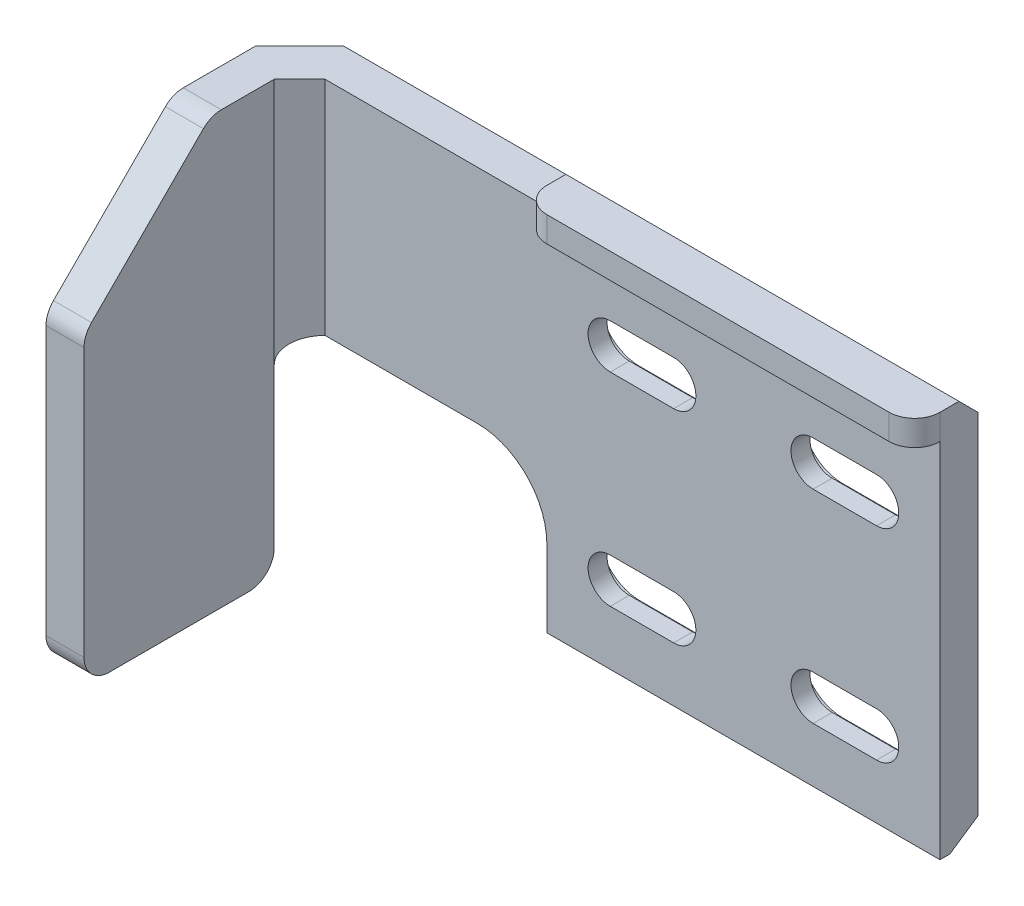
SolidWorks part; units mm, degrees
ref_plane "Front Plane" through (0, 0, 0) normal (0, 0, 1) x (1, 0, 0)
ref_plane "Top Plane" through (0, 0, 0) normal (0, 1, 0) x (1, 0, 0)
ref_plane "Right Plane" through (0, 0, 0) normal (1, 0, 0) x (0, 0, -1)
sketch "Sketch1" plane through (0, 0, 0) normal (0, 0, 1) x (1, 0, 0)
  line L0 (0, 15.9158) -> (0, -13.0842) construction
  line L5 (-25, 15.9158) -> (25, 15.9158) construction
  line L7 (-8, 31.9158) -> (8, 31.9158) construction
  line L8 (-8, 31.9158) -> (-8, 15.9158) construction
  line L9 (-8, 15.9158) -> (8, 15.9158) construction
  line L10 (8, 31.9158) -> (8, 15.9158) construction
  line L11 (-8, 31.9158) -> (8, 15.9158) construction
  line L12 (-8, 15.9158) -> (8, 31.9158) construction
  line L13 (-8, -13.0842) -> (8, -13.0842) construction
  line L14 (-8, -13.0842) -> (-8, -29.0842) construction
  line L15 (-8, -29.0842) -> (8, -29.0842) construction
  line L16 (8, -13.0842) -> (8, -29.0842) construction
  line L17 (-8, -13.0842) -> (8, -29.0842) construction
  line L18 (-8, -29.0842) -> (8, -13.0842) construction
  line L19 (0, -13.0842) -> (0, -16.0842) construction
  line L20 (-16.5, -16.0842) -> (16.5, -16.0842) construction
  line L21 (-25, 15.9158) -> (-25, -16.0842) construction
  line L22 (-25, -16.0842) -> (-16.5, -16.0842) construction
  line L23 (-8, 31.9158) -> (-38, 31.9158) construction
  line L24 (38, 38.9158) -> (-38, 38.9158)
  line L25 (38, 38.9158) -> (38, -36.0842) construction
  line L26 (38, -36.0842) -> (-38, -36.0842) construction
  line L27 (-38, 38.9158) -> (-38, -36.0842) construction
  line L28 (8, 31.9158) -> (38, 31.9158) construction
  line L29 (8, 31.9158) -> (8, 38.9158) construction
  line L30 (8, -29.0842) -> (8, -36.0842) construction
  line L31 (-10.5, 31.9158) -> (-5.5, 31.9158) construction
  line L34 (-10.5, 33.6658) -> (-5.5, 33.6658)
  line L37 (-10.5, 30.1658) -> (-5.5, 30.1658)
  line L38 (5.5, 31.9158) -> (10.5, 31.9158) construction
  line L39 (5.5, 33.6658) -> (10.5, 33.6658)
  line L40 (5.5, 30.1658) -> (10.5, 30.1658)
  line L41 (5.5, 15.9158) -> (10.5, 15.9158) construction
  line L42 (5.5, 17.6658) -> (10.5, 17.6658)
  line L43 (5.5, 14.1658) -> (10.5, 14.1658)
  line L44 (-10.5, 15.9158) -> (-5.5, 15.9158) construction
  line L45 (-10.5, 17.6658) -> (-5.5, 17.6658)
  line L46 (-10.5, 14.1658) -> (-5.5, 14.1658)
  line L47 (-38, 38.9158) -> (-38, 9.8549)
  line L48 (-38, 9.8549) -> (38, 9.8549) construction
  line L49 (38, 9.8549) -> (38, 38.9158)
  line L50 (-36.8222, 31.9158) -> (-36.8222, 9.9158) construction
  line L51 (-29, 15.9158) -> (-21, 15.9158) construction
  line L54 (-29, 21.4158) -> (-21, 21.4158) construction
  line L57 (-29, 10.4158) -> (-21, 10.4158) construction
  line L58 (21, 15.9158) -> (29, 15.9158) construction
  line L59 (21, 21.4158) -> (29, 21.4158) construction
  line L60 (21, 10.4158) -> (29, 10.4158) construction
  line L61 (-29, 21.4158) -> (-21, 21.4158)
  line L62 (-34.5, 15.9158) -> (-34.5, 9.8549)
  line L63 (-34.5, 9.8549) -> (-38, 9.8549)
  line L64 (-15.5, 15.9158) -> (-15.5, 9.8549)
  line L65 (15.5, 15.9158) -> (15.5, 9.8549)
  line L66 (15.5, 9.8549) -> (-15.5, 9.8549)
  line L67 (34.5, 15.9158) -> (34.5, 9.8549)
  line L68 (34.5, 9.8549) -> (38, 9.8549)
  line L69 (21, 21.4158) -> (29, 21.4158)
  line L70 (-29, 21.4158) -> (-34.5, 21.4158)
  line L71 (-34.5, 21.4158) -> (-34.5, 15.9158)
  line L72 (29, 21.4158) -> (34.5, 21.4158) construction
  line L73 (34.5, 21.4158) -> (34.5, 15.9158) construction
  circle A0 centre (-8, 31.9158) radius 1.75 construction
  circle A1 centre (8, 31.9158) radius 1.75 construction
  circle A2 centre (8, 15.9158) radius 1.75 construction
  circle A3 centre (-8, 15.9158) radius 1.75 construction
  circle A4 centre (-8, -13.0842) radius 1.75 construction
  circle A5 centre (8, -13.0842) radius 1.75 construction
  circle A6 centre (8, -29.0842) radius 1.75 construction
  circle A7 centre (-8, -29.0842) radius 1.75 construction
  circle A8 centre (-25, 15.9158) radius 5.5 construction
  circle A9 centre (25, 15.9158) radius 5.5 construction
  circle A10 centre (-16.5, -16.0842) radius 5.5 construction
  circle A11 centre (16.5, -16.0842) radius 5.5 construction
  arc A16 (-10.5, 33.6658) -> (-10.5, 30.1658) centre (-10.5, 31.9158) ccw
  arc A17 (-5.5, 30.1658) -> (-5.5, 33.6658) centre (-5.5, 31.9158) ccw
  arc A18 (5.5, 33.6658) -> (5.5, 30.1658) centre (5.5, 31.9158) ccw
  arc A19 (10.5, 30.1658) -> (10.5, 33.6658) centre (10.5, 31.9158) ccw
  arc A20 (5.5, 17.6658) -> (5.5, 14.1658) centre (5.5, 15.9158) ccw
  arc A21 (10.5, 14.1658) -> (10.5, 17.6658) centre (10.5, 15.9158) ccw
  arc A22 (-10.5, 17.6658) -> (-10.5, 14.1658) centre (-10.5, 15.9158) ccw
  arc A23 (-5.5, 14.1658) -> (-5.5, 17.6658) centre (-5.5, 15.9158) ccw
  arc A28 (-29, 21.4158) -> (-29, 10.4158) centre (-29, 15.9158) ccw construction
  arc A29 (-21, 10.4158) -> (-21, 21.4158) centre (-21, 15.9158) ccw construction
  arc A30 (21, 21.4158) -> (21, 10.4158) centre (21, 15.9158) ccw construction
  arc A31 (29, 10.4158) -> (29, 21.4158) centre (29, 15.9158) ccw construction
  arc A32 (21, 21.4158) -> (15.5, 15.9158) centre (21, 15.9158) ccw
  arc A34 (-21, 21.4158) -> (-15.5, 15.9158) centre (-21, 15.9158) cw
  arc A37 (29, 21.4158) -> (34.5, 15.9158) centre (29, 15.9158) cw
  point P5 (0, 15.9158)
  point P8 (0, 23.9158)
  point P13 (0, -21.0842)
  point P31 (0, -16.0842)
  point P42 (-8, 31.9158)
  point P49 (8, 31.9158)
  point P56 (8, 15.9158)
  point P63 (-8, 15.9158)
  point P75 (-25, 15.9158)
  point P81 (25, 15.9158)
  dimension "D2" = 3.5
  dimension "D5" = 11
  dimension "D11" = 76
  dimension "D12" = 22
  dimension "D1" = 16
  dimension "D3" = 29
  dimension "D4" = 32
  dimension "D6" = 30
  dimension "D7" = 75
  dimension "D8" = 7
  dimension "D9" = 33
  dimension "D10" = 50
extrude "Boss-Extrude1" add sketch "Sketch1" along normal blind 3
sketch "Sketch2" plane through (0, 0, 3) normal (0, 0, 1) x (1, 0, 0)
  line L0 (38, 38.9158) -> (-38, 38.9158) construction
  line L1 (-38, 38.9158) -> (-35, 38.9158)
  line L2 (-38, 38.9158) -> (-38, 4.9158)
  line L3 (-38, 4.9158) -> (-35, 4.9158)
  line L4 (-35, 38.9158) -> (-35, 4.9158)
  dimension "D1" = 34
  dimension "D2" = 3
extrude "Boss-Extrude2" add sketch "Sketch2" along normal blind 17 and the other way up to vertex (3 mm away) other way up to point (-38, 9.8549, 0)
sketch "Sketch3" plane through (0, 0, 3) normal (0, 0, 1) x (1, 0, 0)
  line L1 (38, 38.9158) -> (15.5, 38.9158)
  line L2 (38, 38.9158) -> (38, 9.8549)
  line L3 (38, 9.8549) -> (15.5, 9.8549)
  line L4 (15.5, 38.9158) -> (15.5, 9.8549)
extrude "Cut-Extrude1" cut sketch "Sketch3" against normal blind 18
sketch "Sketch4" plane through (0, 0, 0) normal (0, 0, -1) x (-1, 0, 0)
  line L0 (4.8, 31.9158) -> (11.2, 31.9158) construction
  line L1 (4.8, 35.1158) -> (11.2, 35.1158)
  line L2 (4.8, 28.7158) -> (11.2, 28.7158)
  line L3 (-8, 33.6658) -> (-8, 30.1658) construction
  line L4 (-10.5, 33.6658) -> (-5.5, 33.6658) construction
  line L5 (-5.5, 30.1658) -> (-10.5, 30.1658) construction
  line L6 (-8, 17.6658) -> (-8, 14.1658) construction
  line L7 (-10.5, 17.6658) -> (-5.5, 17.6658) construction
  line L8 (-5.5, 14.1658) -> (-10.5, 14.1658) construction
  line L9 (8, 33.6658) -> (8, 30.1658) construction
  line L10 (5.5, 33.6658) -> (10.5, 33.6658) construction
  line L11 (10.5, 30.1658) -> (5.5, 30.1658) construction
  line L12 (8, 17.6658) -> (8, 14.1658) construction
  line L13 (5.5, 17.6658) -> (10.5, 17.6658) construction
  line L14 (10.5, 14.1658) -> (5.5, 14.1658) construction
  line L15 (-11.2, 31.9158) -> (-4.8, 31.9158) construction
  line L16 (-11.2, 35.1158) -> (-4.8, 35.1158)
  line L17 (-11.2, 28.7158) -> (-4.8, 28.7158)
  line L18 (4.8, 15.9158) -> (11.2, 15.9158) construction
  line L19 (4.8, 19.1158) -> (11.2, 19.1158)
  line L20 (4.8, 12.7158) -> (11.2, 12.7158)
  line L21 (-11.2, 15.9158) -> (-4.8, 15.9158) construction
  line L22 (-11.2, 19.1158) -> (-4.8, 19.1158)
  line L23 (-11.2, 12.7158) -> (-4.8, 12.7158)
  arc A0 (4.8, 35.1158) -> (4.8, 28.7158) centre (4.8, 31.9158) ccw
  arc A1 (11.2, 28.7158) -> (11.2, 35.1158) centre (11.2, 31.9158) ccw
  arc A2 (-11.2, 35.1158) -> (-11.2, 28.7158) centre (-11.2, 31.9158) ccw
  arc A3 (-4.8, 28.7158) -> (-4.8, 35.1158) centre (-4.8, 31.9158) ccw
  arc A4 (4.8, 19.1158) -> (4.8, 12.7158) centre (4.8, 15.9158) ccw
  arc A5 (11.2, 12.7158) -> (11.2, 19.1158) centre (11.2, 15.9158) ccw
  arc A6 (-11.2, 19.1158) -> (-11.2, 12.7158) centre (-11.2, 15.9158) ccw
  arc A7 (-4.8, 12.7158) -> (-4.8, 19.1158) centre (-4.8, 15.9158) ccw
  point P2 (8, 31.9158)
  point P34 (-8, 31.9158)
  point P40 (8, 15.9158)
  point P47 (-8, 15.9158)
  dimension "D1" = 3.2
  dimension "D2" = 6.4
extrude "Cut-Extrude2" cut sketch "Sketch4" against normal blind 1.5
chamfer "Chamfer1" distance 10 angle 45 1 edges at (-36.5, 38.9158, 20)
chamfer "Chamfer2" distance 1.5 angle 56 1 edges at (0, 9.8549, 0)
sketch "Sketch7" plane through (0, 0, 3) normal (0, 0, 1) x (1, 0, 0)
  line L0 (-15.5, 9.8549) -> (-15.5, 38.4158) construction
  line L1 (15.5, 38.9158) -> (-15.5, 38.9158) construction
  line L2 (15.5, 38.9158) -> (15.5, 38.4158) construction
  line L3 (15.5, 38.4158) -> (-15.5, 38.4158) construction
  line L4 (-15.5, 38.9158) -> (-15.5, 38.4158) construction
  line L5 (-15.5, 38.4158) -> (15.5, 38.4158)
  line L6 (-15.5, 38.4158) -> (-15.5, 40.4158)
  line L7 (-15.5, 40.4158) -> (15.5, 40.4158)
  line L8 (15.5, 38.4158) -> (15.5, 40.4158)
  dimension "D1" = 0.5
  dimension "D2" = 2
  dimension "D3" = 31
extrude "Boss-Extrude3" add sketch "Sketch7" along normal blind 2 and the other way up to vertex (3 mm away)
sketch "Sketch9" plane through (0, 0, 0) normal (0, 0, -1) x (-1, 0, 0)
  line L1 (35, 9.8549) -> (34.5, 9.8549)
  line L2 (35, 9.8549) -> (35, 21.4158)
  line L3 (35, 21.4158) -> (34.5, 21.4158)
  line L4 (34.5, 9.8549) -> (34.5, 21.4158)
extrude "Cut-Extrude4" cut sketch "Sketch9" against normal blind 10
chamfer "Chamfer3" distance 1.5 angle 45 1 edges at (0, 40.4158, 0)
sketch "Sketch11" plane through (0, 4.9158, 0) normal (0, -1, 0) x (-1, 0, 0)
  line L0 (35, 0) -> (35, -20) construction
  line L1 (38, 0) -> (35, 0)
  line L2 (38, 0) -> (38, -5)
  line L3 (38, -5) -> (35, -5)
  line L4 (35, 0) -> (35, -5)
extrude "Cut-Extrude6" cut sketch "Sketch11" against normal up to vertex
chamfer "Chamfer9" distance 2 angle 45 1 edges at (-35, 30.1658, 3)
chamfer "Chamfer10" distance 3.5 angle 45 1 edges at (-38, 30.1658, 0)
fillet "Fillet2" radius 2 7 edges at (-36.5, 21.4158, 5) (-36.5, 38.9158, 10) (-36.5, 28.9158, 20) (-36.5, 4.9158, 20) (-36.5, 4.9158, 5) (-15.5, 39.4158, 5) (15.5, 39.4158, 5)
sketch "Sketch12" plane through (0, 0, 0) normal (0, 0, -1) x (-1, 0, 0)
  line L0 (-20.4205, 13.0403) -> (-20.4205, 35.9822) construction
  line L1 (-12.4498, 13.0403) -> (-20.4205, 13.0403)
  line L2 (-12.4498, 13.0403) -> (-12.4498, 5.0696)
  line L3 (-12.4498, 5.0696) -> (-20.4205, 5.0696)
  line L4 (-20.4205, 13.0403) -> (-20.4205, 5.0696)
  line L5 (14.1903, 13.5314) -> (22.1611, 13.5314)
  line L6 (14.1903, 13.5314) -> (14.1903, 5.5606)
  line L7 (14.1903, 5.5606) -> (22.1611, 5.5606)
  line L8 (22.1611, 13.5314) -> (22.1611, 5.5606)
  line L9 (-12.4498, 35.9822) -> (-20.4205, 35.9822)
  line L10 (-12.4498, 35.9822) -> (-12.4498, 43.9529)
  line L11 (-12.4498, 43.9529) -> (-20.4205, 43.9529)
  line L12 (-20.4205, 35.9822) -> (-20.4205, 43.9529)
extrude "Boss-Extrude4" [suppressed] add sketch "Sketch12" against normal blind 0.25
